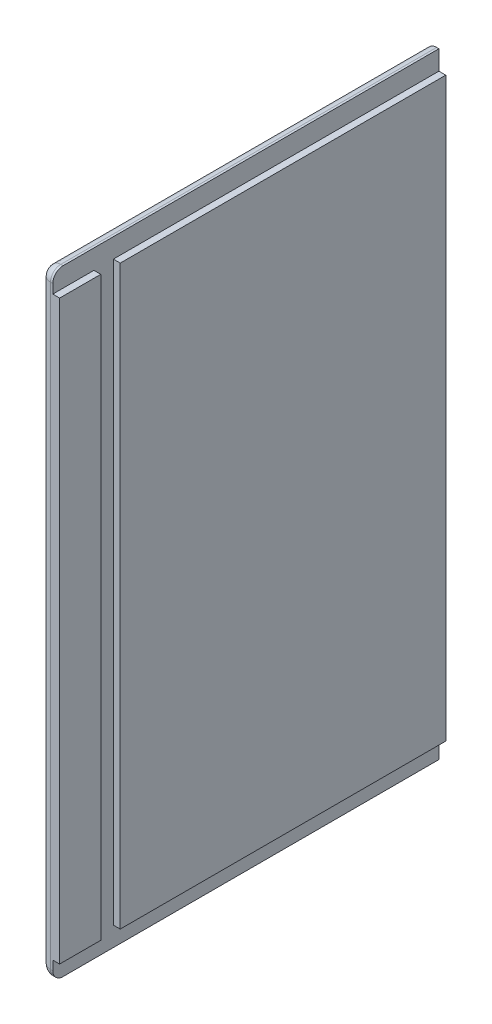
SolidWorks part; units mm, degrees
ref_plane "Front Plane" through (0, 0, 0) normal (0, 0, 1) x (1, 0, 0)
ref_plane "Top Plane" through (0, 0, 0) normal (0, 1, 0) x (1, 0, 0)
ref_plane "Right Plane" through (0, 0, 0) normal (1, 0, 0) x (0, 0, -1)
sketch "Sketch1" plane through (0, 0, 0) normal (1, 0, 0) x (0, 0, -1)
  line L1 (0, 0) -> (357.5, 0)
  line L2 (0, 0) -> (0, 570)
  line L3 (0, 570) -> (357.5, 570)
  line L4 (357.5, 0) -> (357.5, 570)
  dimension "D1" = 357.5
  dimension "D2" = 570
extrude "Boss-Extrude1" add sketch "Sketch1" along normal blind 18
sketch "Sketch5" plane through (18, 0, 0) normal (1, 0, 0) x (0, 0, -1)
  line L0 (0, 570) -> (0, 0) construction
  line L1 (56.1, 563.65) -> (38.1, 563.65)
  line L2 (56.1, 563.65) -> (56.1, 6.35)
  line L3 (56.1, 6.35) -> (38.1, 6.35)
  line L4 (38.1, 563.65) -> (38.1, 6.35)
  line L5 (0, 0) -> (357.5, 0) construction
  line L6 (357.5, 570) -> (0, 570) construction
  dimension "D1" = 18
  dimension "D2" = 38.1
  dimension "D3" = 6.35
  dimension "D4" = 6.35
extrude "Cut-Extrude3" cut sketch "Sketch5" against normal blind 6.35
sketch "Sketch6" plane through (18, 0, 0) normal (1, 0, 0) x (0, 0, -1)
  line L0 (357.5, 0) -> (357.5, 570) construction
  line L1 (357.5, 563.65) -> (344.8, 563.65)
  line L2 (357.5, 563.65) -> (357.5, 6.35)
  line L3 (357.5, 6.35) -> (344.8, 6.35)
  line L4 (344.8, 563.65) -> (344.8, 6.35)
  line L5 (0, 0) -> (357.5, 0) construction
  line L6 (357.5, 570) -> (0, 570) construction
  dimension "D1" = 12.7
  dimension "D2" = 6.35
  dimension "D3" = 6.35
sketch "Sketch7" plane through (18, 0, 0) normal (1, 0, 0) x (0, 0, -1)
  line L0 (357.5, 563.65) -> (357.5, 6.35) construction
  line L1 (0, 0) -> (357.5, 0)
  line L2 (0, 0) -> (0, 18)
  line L3 (0, 18) -> (357.5, 18)
  line L4 (357.5, 0) -> (357.5, 18)
  line L6 (0, 570) -> (357.5, 570)
  line L7 (0, 570) -> (0, 552)
  line L8 (0, 552) -> (357.5, 552)
  line L9 (357.5, 570) -> (357.5, 552)
  dimension "D1" = 18
  dimension "D2" = 18
extrude "Cut-Extrude4" cut sketch "Sketch7" against normal blind 6.35
fillet "Fillet1" radius 9.525 5 edges at (0, 0, -178.75) (0, 285, 0) (0, 570, -178.75) (5.825, 0, 0) (5.825, 570, 0)
